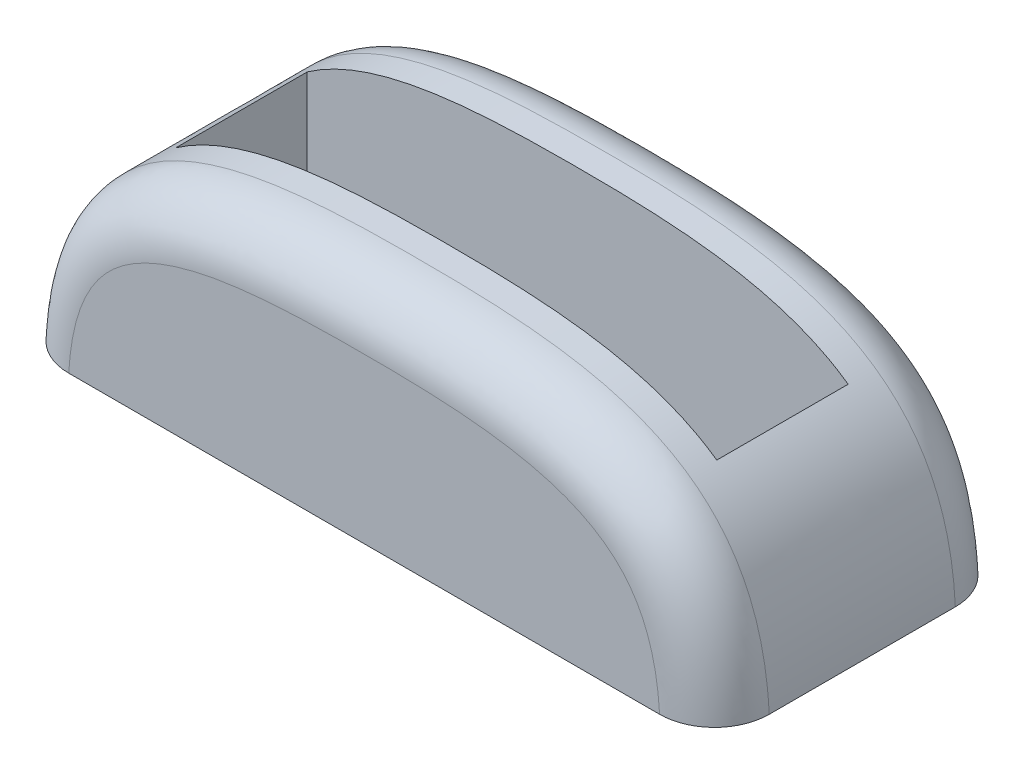
SolidWorks part; units mm, degrees
ref_plane "Front Plane" through (0, 0, 0) normal (0, 0, 1) x (1, 0, 0)
ref_plane "Top Plane" through (0, 0, 0) normal (0, 1, 0) x (1, 0, 0)
ref_plane "Right Plane" through (0, 0, 0) normal (1, 0, 0) x (0, 0, -1)
sketch "Sketch1" plane through (0, 0, 0) normal (0, 1, 0) x (1, 0, 0)
  line L1 (-9.88, -2.4) -> (9.88, -2.4)
  line L2 (-9.88, -2.4) -> (-9.88, 2.4)
  line L3 (-9.88, 2.4) -> (9.88, 2.4)
  line L4 (9.88, -2.4) -> (9.88, 2.4)
  line L5 (-9.88, -2.4) -> (9.88, 2.4) construction
  line L6 (-9.88, 2.4) -> (9.88, -2.4) construction
  line L7 (-12.795, 5.4) -> (12.795, 5.4)
  line L8 (-12.795, 5.4) -> (-12.795, -5.4)
  line L9 (-12.795, -5.4) -> (12.795, -5.4)
  line L10 (12.795, 5.4) -> (12.795, -5.4)
  line L11 (-12.795, 5.4) -> (12.795, -5.4) construction
  line L12 (-12.795, -5.4) -> (12.795, 5.4) construction
  point P0 (0, 0)
  point P6 (0, 0)
  dimension "D1" = 4.8
  dimension "D2" = 19.76
  dimension "D3" = 10.8
  dimension "D4" = 25.59
extrude "Boss-Extrude1" add sketch "Sketch1" along normal blind 8
sketch "Sketch2" plane through (0, 0, 5.4) normal (0, 0, 1) x (1, 0, 0)
  line L3 (-12.795, 0) -> (-12.795, 8)
  line L4 (-7, 0) -> (7, 0) construction
  line L5 (-7, 0) -> (-7, 6) construction
  line L6 (-7, 6) -> (7, 6) construction
  line L7 (7, 0) -> (7, 6) construction
  line L8 (-12.795, 8) -> (12.795, 8)
  line L9 (12.795, 8) -> (12.795, 0)
  line L10 (-12.795, 0) -> (12.795, 0)
  point P7 (0, 6)
  point P8 (0, 0)
  dimension "D1" = 6
  dimension "D2" = 14
sketch "Sketch4" plane through (0, 0, 5.4) normal (0, 0, 1) x (1, 0, 0)
  line L0 (-12.795, 8) -> (12.795, 8) construction
  line L1 (-10, 6) -> (10, 6) construction
  line L2 (-10, 6) -> (-10, 0) construction
  line L3 (-10, 0) -> (10, 0) construction
  line L4 (10, 6) -> (10, 0) construction
  line L5 (12.795, 8) -> (12.795, 0) construction
  line L6 (-12.795, 0) -> (12.795, 0) construction
  line L7 (-12.795, 0) -> (-12.795, 9.1315)
  line L8 (-12.795, 9.1315) -> (12.795, 9.1315)
  line L9 (12.795, 9.1315) -> (12.795, 0)
  spline S0 degree 3 poles (-12.795, 0) (-12.4266, 7.5025) (0, 8.4975) (12.4266, 7.5025) (12.795, 0) knots 0 0 0 0 0.5 1 1 1 1
  point P4 (0, 0)
  dimension "D1" = 6
  dimension "D2" = 20
sketch "Sketch3" plane through (0, 0, 0) normal (0, -1, 0) x (1, 0, 0)
  line L1 (12, 4.4) -> (-12, 4.4)
  line L2 (12, 4.4) -> (12, -4.4)
  line L3 (12, -4.4) -> (-12, -4.4)
  line L4 (-12, 4.4) -> (-12, -4.4)
  point P4 (12, 0)
  point P5 (0, 4.4)
  dimension "D1" = 24
  dimension "D2" = 8.8
extrude "Cut-Extrude3" cut sketch "Sketch4" against normal through all
fillet "Fillet2" radius 2 1 edges
fillet "Fillet3" radius 2 1 edges
extrude "Cut-Extrude2" cut sketch "Sketch3" against normal blind 1
fillet "Fillet4" radius 2 4 edges at (-12, 0.5, 4.4) (12, 0.5, 4.4) (12, 0.5, -4.4) (-12, 0.5, -4.4)
